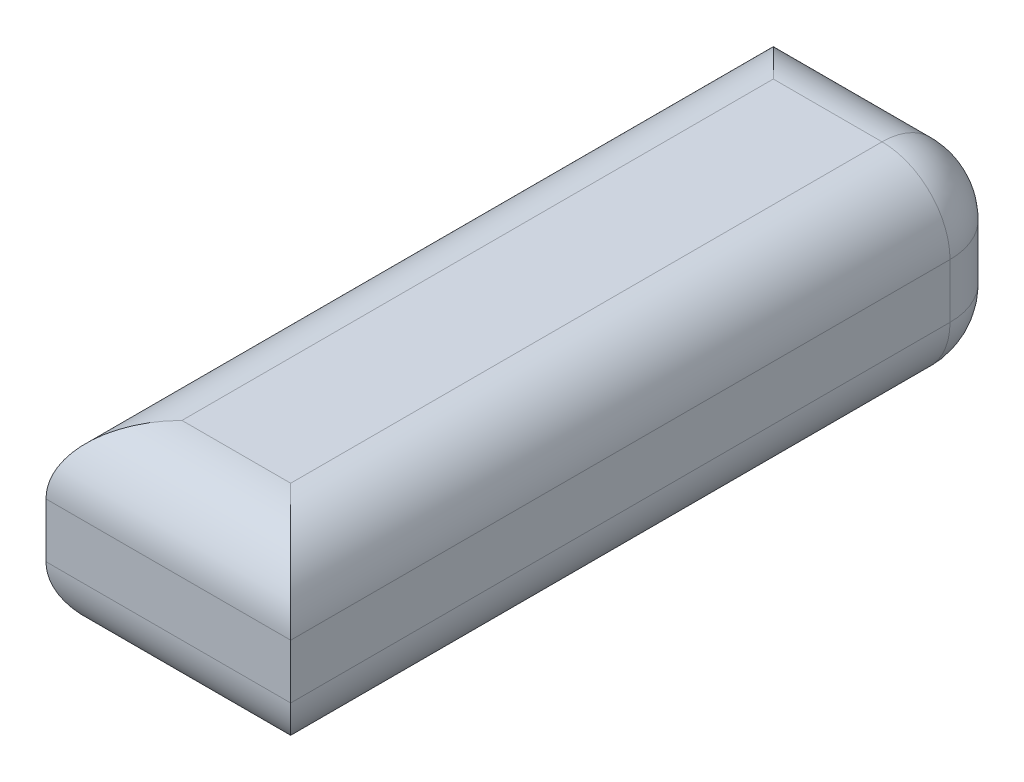
SolidWorks part; units mm, degrees
material "Copper"
ref_plane "Front Plane" through (0, 0, 0) normal (0, 0, 1) x (1, 0, 0)
ref_plane "Top Plane" through (0, 0, 0) normal (0, 1, 0) x (1, 0, 0)
ref_plane "Right Plane" through (0, 0, 0) normal (1, 0, 0) x (0, 0, -1)
sketch "Sketch1" plane through (0, 0, 0) normal (0, 1, 0) x (1, 0, 0)
  line L1 (0, 0) -> (36, 0)
  line L2 (0, 0) -> (0, 107)
  line L3 (0, 107) -> (36, 107)
  line L4 (36, 0) -> (36, 107)
  dimension "D1" = 107
  dimension "D2" = 36
extrude "Boss-Extrude1" add sketch "Sketch1" along normal blind 28
fillet "Fillet1" radius 10 9 edges at (36, 14, -107) (18, 28, -107) (36, 28, -53.5) (36, 0, -53.5) (18, 0, -107) (0, 0, -53.5) (18, 0, 0) (18, 28, 0) (0, 28, -53.5)
